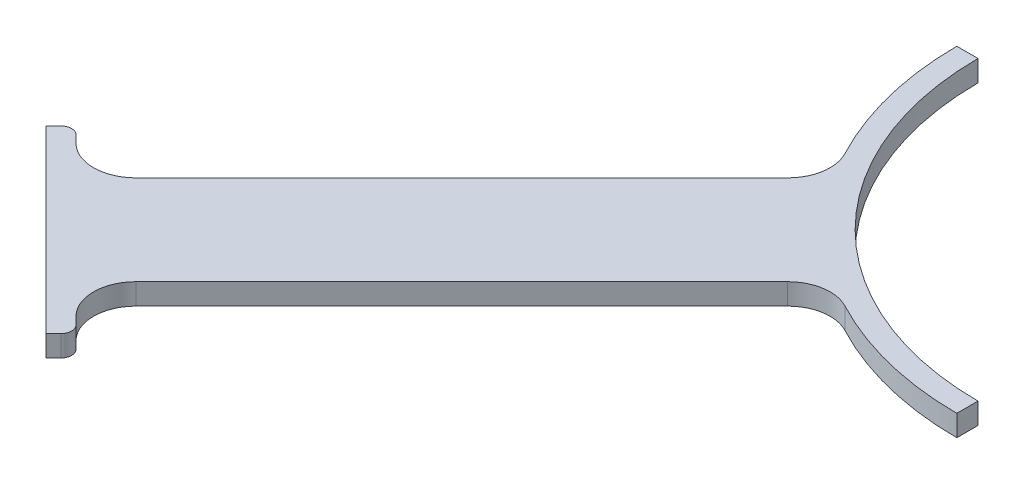
SolidWorks part; units mm, degrees
ref_plane "Front Plane" through (0, 0, 0) normal (0, 0, 1) x (1, 0, 0)
ref_plane "Top Plane" through (0, 0, 0) normal (0, 1, 0) x (1, 0, 0)
ref_plane "Right Plane" through (0, 0, 0) normal (1, 0, 0) x (0, 0, -1)
sketch "Sketch2" plane through (0, 0, 0) normal (0, 1, 0) x (1, 0, 0)
  line L0 (-70, 0) -> (-75, 0)
  line L1 (0, -70) -> (0, -75)
  line L3 (-144.9569, -144.9569) -> (-166.1701, -123.7437)
  line L4 (-144.9569, -144.9569) -> (-123.7437, -166.1701)
  line L7 (-152.028, -130.8148) -> (-62.5681, -41.3549)
  line L8 (-130.8148, -152.028) -> (-41.3549, -62.5681)
  line L9 (-166.1701, -123.7437) -> (-162.6346, -120.2082)
  line L10 (-162.6346, -120.2082) -> (-152.028, -130.8148)
  line L11 (-123.7437, -166.1701) -> (-120.2082, -162.6346)
  line L12 (-120.2082, -162.6346) -> (-130.8148, -152.028)
  arc A0 (-70, 0) -> (0, -70) centre (0, 0) ccw
  arc A1 (-75, 0) -> (0, -75) centre (0, 0) ccw
extrude "Boss-Extrude1" add sketch "Sketch2" along normal blind 5 contours L0 A1 L1 A0 | A1 L7 L10 L9 L3 L4 L11 L12 L8
fillet "Fillet1" radius 10 4 edges at (-130.8148, 2.5, 152.028) (-152.028, 2.5, 130.8148) (-62.5681, 2.5, 41.3549) (-41.3549, 2.5, 62.5681)
fillet "Fillet2" radius 2.5 2 edges at (-120.2082, 2.5, 162.6346) (-162.6346, 2.5, 120.2082)
